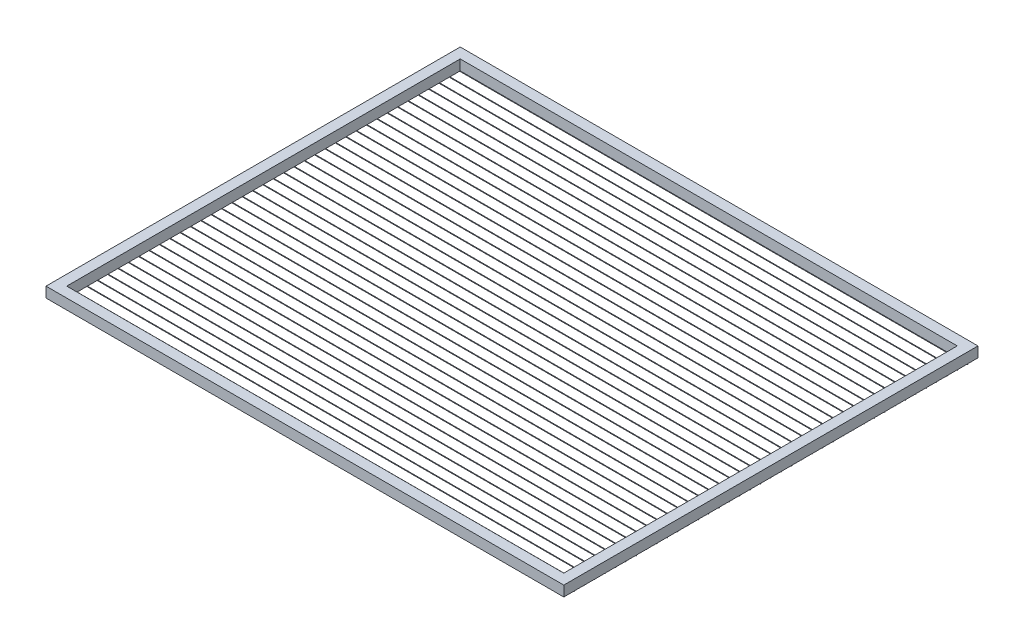
SolidWorks part; units mm, degrees
ref_plane "Front Plane" through (0, 0, 0) normal (0, 0, 1) x (1, 0, 0)
ref_plane "Top Plane" through (0, 0, 0) normal (0, 1, 0) x (1, 0, 0)
ref_plane "Right Plane" through (0, 0, 0) normal (1, 0, 0) x (0, 0, -1)
sketch "Sketch1" plane through (0, 0, 0) normal (0, 1, 0) x (1, 0, 0)
  line L0 (-240, 190) -> (240, 190)
  line L1 (-250, -200) -> (250, -200)
  line L2 (-250, -200) -> (-250, 200)
  line L3 (-250, 200) -> (250, 200)
  line L4 (250, -200) -> (250, 200)
  line L5 (-250, -200) -> (250, 200) construction
  line L6 (-250, 200) -> (250, -200) construction
  line L7 (240, -190) -> (240, 190)
  line L8 (-240, -190) -> (240, -190)
  line L9 (-240, -190) -> (-240, 190)
  point P0 (0, 0)
  dimension "D1" = 400
  dimension "D2" = 500
  dimension "D3" = 10
extrude "Boss-Extrude1" add sketch "Sketch1" along normal blind 10
sketch "Sketch3" plane through (250, 0, 0) normal (1, 0, 0) x (0, 0, -1)
  circle A0 centre (0, -0.25) radius 0.25
  circle A1 centre (-10, -0.25) radius 0.25
  circle A2 centre (-20, -0.25) radius 0.25
  circle A3 centre (-30, -0.25) radius 0.25
  circle A4 centre (-40, -0.25) radius 0.25
  circle A5 centre (-50, -0.25) radius 0.25
  circle A6 centre (-60, -0.25) radius 0.25
  circle A7 centre (-70, -0.25) radius 0.25
  circle A8 centre (-80, -0.25) radius 0.25
  circle A9 centre (-90, -0.25) radius 0.25
  circle A10 centre (-100, -0.25) radius 0.25
  circle A11 centre (-110, -0.25) radius 0.25
  circle A12 centre (-120, -0.25) radius 0.25
  circle A13 centre (-130, -0.25) radius 0.25
  circle A14 centre (-140, -0.25) radius 0.25
  circle A15 centre (-150, -0.25) radius 0.25
  circle A16 centre (-160, -0.25) radius 0.25
  circle A17 centre (-170, -0.25) radius 0.25
  circle A18 centre (-180, -0.25) radius 0.25
  circle A19 centre (-190, -0.25) radius 0.25
  circle A20 centre (10, -0.25) radius 0.25
  circle A21 centre (20, -0.25) radius 0.25
  circle A22 centre (30, -0.25) radius 0.25
  circle A23 centre (40, -0.25) radius 0.25
  circle A24 centre (50, -0.25) radius 0.25
  circle A25 centre (60, -0.25) radius 0.25
  circle A26 centre (70, -0.25) radius 0.25
  circle A27 centre (80, -0.25) radius 0.25
  circle A28 centre (90, -0.25) radius 0.25
  circle A29 centre (100, -0.25) radius 0.25
  circle A30 centre (110, -0.25) radius 0.25
  circle A31 centre (120, -0.25) radius 0.25
  circle A32 centre (130, -0.25) radius 0.25
  circle A33 centre (140, -0.25) radius 0.25
  circle A34 centre (150, -0.25) radius 0.25
  circle A35 centre (160, -0.25) radius 0.25
  circle A36 centre (170, -0.25) radius 0.25
  circle A37 centre (180, -0.25) radius 0.25
  circle A38 centre (190, -0.25) radius 0.25
  dimension "D2" = 20
  dimension "D1" = 20
extrude "Boss-Extrude2" add sketch "Sketch3" against normal up to surface (500 mm away) separate body up to face at (-250, 5, 0)
